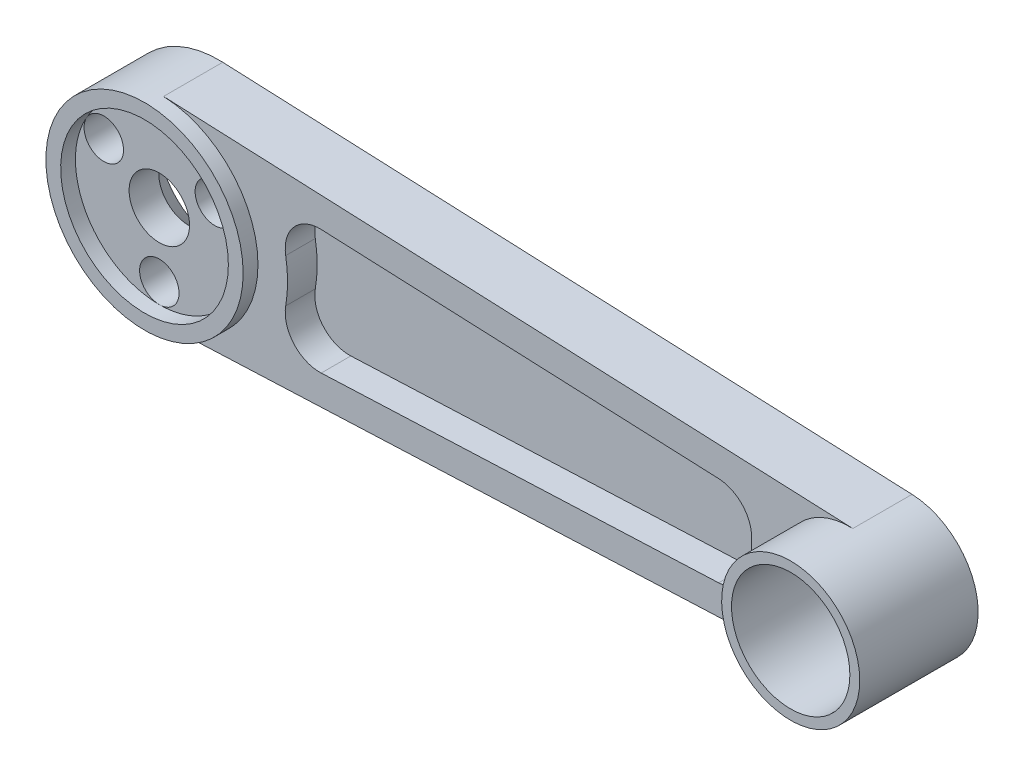
SolidWorks part; units mm, degrees
material "6061-T6 (SS)"
ref_plane "Front Plane" through (0, 0, 0) normal (0, 0, 1) x (1, 0, 0)
ref_plane "Top Plane" through (0, 0, 0) normal (0, 1, 0) x (1, 0, 0)
ref_plane "Right Plane" through (0, 0, 0) normal (1, 0, 0) x (0, 0, -1)
sketch "Sketch1" plane through (0, 0, 0) normal (0, 0, 1) x (1, 0, 0)
  line L0 (0.4286, -9.9908) -> (70.3, -6.9936)
  line L1 (70.3, 6.9936) -> (0.4286, 9.9908)
  circle A0 centre (0, 0) radius 3.0625
  circle A3 centre (0, 0) radius 3.0625
  circle A5 centre (0, 0) radius 3.0625
  circle A6 centre (70, 0) radius 6
  circle A7 centre (70, 0) radius 7
  circle A8 centre (0, 0) radius 10
  point P12 (0, 0)
  point P15 (0, 0)
  dimension "D2" = 6.125
  dimension "D5" = 12
  dimension "D6" = 14
  dimension "D7" = 20
  dimension "D4" = 70
  dimension "D8" = 3
extrude "Boss-Extrude1" add sketch "Sketch1" along normal blind 6
sketch "Sketch2" plane through (0, 0, 6) normal (0, 0, 1) x (1, 0, 0)
  circle A0 centre (0, -6.5) radius 2
  circle A1 centre (0, 0) radius 3.0625 construction
  circle A2 centre (-5.6292, 3.25) radius 2
  circle A3 centre (5.6292, 3.25) radius 2
  point P10 (0, 0)
  dimension "D1" = 4
  dimension "D2" = 6.5
  dimension "D3" = 3
extrude "Cut-Extrude1" cut sketch "Sketch2" against normal blind 4.5
sketch "Sketch3" plane through (0, 0, 6) normal (0, 0, 1) x (1, 0, 0)
  circle A0 centre (0, 0) radius 10
  circle A1 centre (0, 0) radius 8.5
  arc A2 (0.4286, 9.9908) -> (0.4286, -9.9908) centre (0, 0) ccw construction
  dimension "D1" = 17
extrude "Boss-Extrude2" add sketch "Sketch3" along normal blind 1.5
chamfer "Chamfer1" distance 3 angle 45 1 edges at (3.0625, 0, 0)
sketch "Sketch4" plane through (0, 0, 6) normal (0, 0, 1) x (1, 0, 0)
  circle A0 centre (70, 0) radius 6
  circle A1 centre (70, 0) radius 7
  circle A2 centre (70, 0) radius 6 construction
  arc A3 (70.3, -6.9936) -> (70.3, 6.9936) centre (70, 0) ccw construction
extrude "Boss-Extrude3" add sketch "Sketch4" along normal blind 6
sketch "Sketch5" plane through (0, 0, 6) normal (0, 0, 1) x (1, 0, 0)
  line L0 (16.4097, -6.3025) -> (56.6931, -4.5745)
  line L1 (16.4097, 6.3025) -> (56.6931, 4.5745)
  line L2 (70.3, 6.9936) -> (0.4286, 9.9908) construction
  line L3 (0.4286, -9.9908) -> (70.3, -6.9936) construction
  arc A0 (12.8107, -2.2106) -> (12.8107, 2.2106) centre (0, 0) ccw
  arc A1 (60.0319, -0.7983) -> (60.0319, 0.7983) centre (70, 0) cw
  arc A2 (70.3, 6.9936) -> (70.3, -6.9936) centre (70, 0) ccw construction
  arc A3 (0.4286, -9.9908) -> (0.4286, 9.9908) centre (0, 0) ccw construction
  arc A4 (60.0319, 0.7983) -> (56.6931, 4.5745) centre (56.5431, 1.0777) ccw
  arc A5 (56.6931, -4.5745) -> (60.0319, -0.7983) centre (56.5431, -1.0777) ccw
  arc A6 (16.4097, 6.3025) -> (12.8107, 2.2106) centre (16.2597, 2.8057) ccw
  arc A7 (12.8107, -2.2106) -> (16.4097, -6.3025) centre (16.2597, -2.8057) ccw
  dimension "D3" = 3
  dimension "D4" = 3
  dimension "D5" = 3.5
  dimension "D1" = 3
  dimension "D2" = 3
extrude "Cut-Extrude2" cut sketch "Sketch5" against normal blind 3
